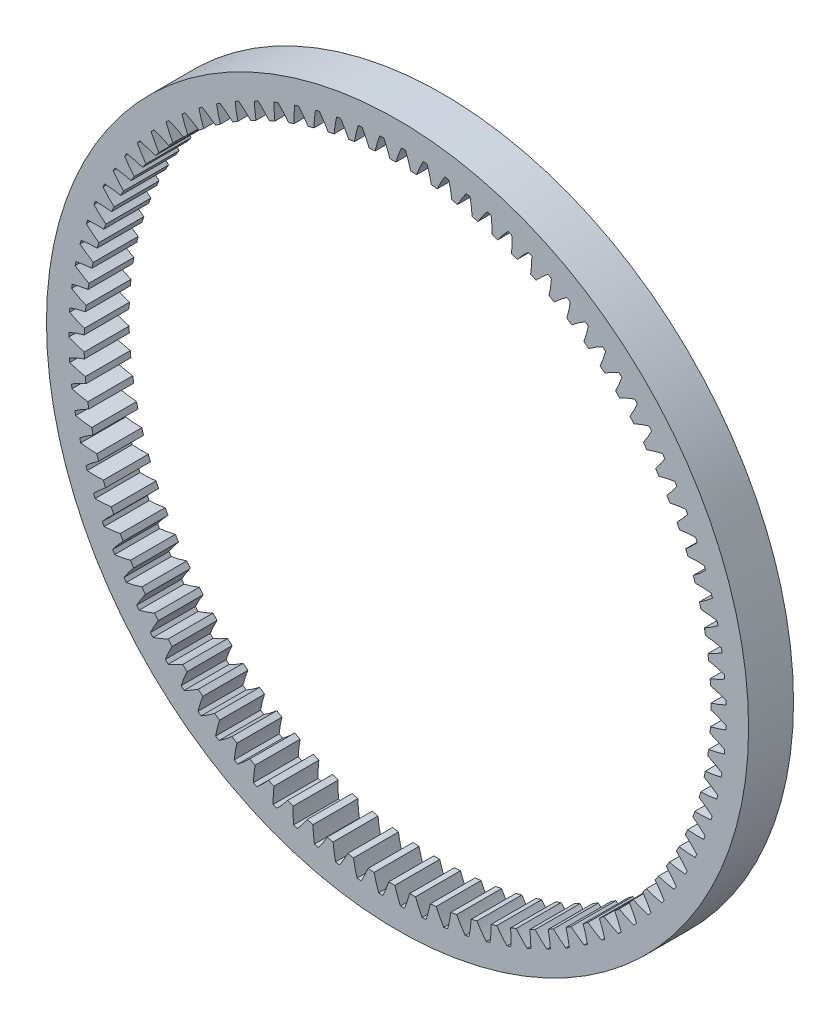
SolidWorks part; units mm, degrees
material "Výchozí"
ref_plane "Rovina XY" through (0, 0, 0) normal (0, 0, 1) x (1, 0, 0)
ref_plane "Rovina XZ" through (0, 0, 0) normal (0, 1, 0) x (1, 0, 0)
ref_plane "Rovina YZ" through (0, 0, 0) normal (1, 0, 0) x (0, 0, -1)
sketch "Skica1" plane through (0, 0, 0) normal (0, 0, 1) x (1, 0, 0)
  line L0 (-7.6722, 0) -> (24.7299, 0) construction
  line L1 (0, 21.5321) -> (0, 42.0656) construction
  line L2 (0, 0) -> (71.2421, 1.0619)
  line L3 (0, 0) -> (71.168, 3.4168)
  line L4 (0, 0) -> (73.0889, 2.2986) construction
  circle A0 centre (0, 0) radius 66.9531
  circle A1 centre (0, 0) radius 69.75
  circle A2 centre (0, 0) radius 71.25 construction
  circle A3 centre (0, 0) radius 73.125
  spline S0 degree 4 poles (66.9531, 0) (66.9836, 0.0005) (67.0692, 0.0035) (67.2309, 0.0154) (67.4941, 0.0435) (67.8284, 0.0923) (68.2589, 0.1701) (68.7635, 0.2807) (69.315, 0.422) (69.911, 0.5969) (70.5019, 0.7901) (71.0872, 0.9999) (71.6668, 1.2248) (72.3632, 1.5146) (73.1926, 1.8887) (74.1482, 2.3598) (75.2219, 2.9406) (76.2936, 3.5715) (77.3431, 4.2379) (78.3713, 4.9379) (79.3771, 5.6679) (80.2395, 6.3331) (80.9633, 6.918) (81.5608, 7.4194) (82.0279, 7.8211) (82.5011, 8.2403) (82.9487, 8.645) (83.4258, 9.0903) (83.8376, 9.481) (84.4371, 10.0683) (84.7907, 10.4245) (85.3537, 11.0015) (85.5975, 11.264) (85.8218, 11.5002) (85.8856, 11.5706) (85.9334, 11.6219) (85.9593, 11.6496) knots 0 0 0 0 0 0.005377 0.015084 0.028532 0.04661 0.064855 0.092111 0.119476 0.146842 0.174209 0.201575 0.228941 0.256307 0.307035 0.361767 0.4165 0.471232 0.525964 0.580697 0.635429 0.690161 0.717528 0.744894 0.77226 0.799626 0.826992 0.854358 0.881725 0.909091 0.954545 0.977273 0.988636 0.994318 1 1 1 1 1 construction
  spline S1 degree 4 poles (66.9531, 0) (66.9836, 0.0005) (67.0692, 0.0035) (67.2309, 0.0154) (67.4941, 0.0435) (67.8284, 0.0923) (68.2589, 0.1701) (68.7635, 0.2807) (69.315, 0.422) (69.911, 0.5969) (70.5019, 0.7901) (71.0872, 0.9999) (71.6668, 1.2248) (72.3632, 1.5146) (73.1926, 1.8887) (74.1482, 2.3598) (75.2219, 2.9406) (76.2936, 3.5715) (77.3431, 4.2379) (78.3713, 4.9379) (79.3771, 5.6679) (80.2395, 6.3331) (80.9633, 6.918) (81.5608, 7.4194) (82.0279, 7.8211) (82.5011, 8.2403) (82.9487, 8.645) (83.4258, 9.0903) (83.8376, 9.481) (84.2235, 9.859) (84.4262, 10.06) (84.5261, 10.1599) knots 0 0 0 0 0 0.005377 0.015084 0.028532 0.04661 0.064855 0.092111 0.119476 0.146842 0.174209 0.201575 0.228941 0.256307 0.307035 0.361767 0.4165 0.471232 0.525964 0.580697 0.635429 0.690161 0.717528 0.744894 0.77226 0.799626 0.826992 0.854358 0.881725 0.909091 0.909091 0.909091 0.909091 0.909091
sketch "Skica2" plane through (0, 0, 0) normal (0, 0, 1) x (1, 0, 0)
  circle A0 centre (0, 0) radius 78.125
  circle A1 centre (0, 0) radius 73.125 construction
  circle A2 centre (0, 0) radius 69.75 construction
  circle A3 centre (0, 0) radius 69.75
  dimension "D1" = 5
extrude "Přidat vysunutím1" add sketch "Skica2" along normal mid plane 10
sketch "Skica3" plane through (0, 0, 5) normal (0, 0, 1) x (1, 0, 0)
  line L0 (0, 0) -> (73.0889, 2.2986) construction
  line L1 (0, 0) -> (73.0889, 2.2986) construction
  circle A0 centre (0, 0) radius 69.75 construction
  circle A1 centre (0, 0) radius 73.125 construction
  arc A2 (69.7478, 0.5512) -> (69.6446, 3.8326) centre (0, 0) ccw
  arc A3 (73.1015, 1.8541) -> (73.0735, 2.7431) centre (0, 0) ccw
  spline S0 degree 4 poles (57.0181, 1999.7686) (60.1184, 35.926) (62.5959, 0.6685) (65.0492, -0.218) (67.4941, 0.0435) (67.8284, 0.0923) (68.2589, 0.1701) (68.7635, 0.2807) (69.315, 0.422) (69.911, 0.5969) (70.5019, 0.7901) (71.0872, 0.9999) (71.6668, 1.2248) (72.3632, 1.5146) (73.1926, 1.8887) (74.1482, 2.3598) (75.2219, 2.9406) (76.2936, 3.5715) (77.3431, 4.2379) (78.3713, 4.9379) (79.3771, 5.6679) (80.2395, 6.3331) (80.9633, 6.918) (81.5608, 7.4194) (82.0279, 7.8211) (82.5011, 8.2403) (82.9487, 8.645) (83.4258, 9.0903) (85.4018, 10.9651) (90.1065, 15.8673) (40.7158, -33.1093) (1497.9964, 1424.7513) knots -0.386327 -0.386327 -0.386327 -0.386327 -0.386327 0.005377 0.015084 0.028532 0.04661 0.064855 0.092111 0.119476 0.146842 0.174209 0.201575 0.228941 0.256307 0.307035 0.361767 0.4165 0.471232 0.525964 0.580697 0.635429 0.690161 0.717528 0.744894 0.77226 0.799626 0.826992 0.854358 0.881725 1.324891 1.324891 1.324891 1.324891 1.324891 only from (66.9531, 0) to (84.5261, 10.1599) construction
  spline S1 degree 4 poles (69.7478, 0.5512) (69.8628, 0.5858) (70.1259, 0.6672) (70.5352, 0.8021) (71.0872, 0.9999) (71.6668, 1.2248) (72.2437, 1.4649) (72.6728, 1.6552) (72.958, 1.7866) (73.1015, 1.8541) knots 0.125702 0.125702 0.125702 0.125702 0.125702 0.146842 0.174209 0.201575 0.228941 0.256307 0.284234 0.284234 0.284234 0.284234 0.284234
  spline S2 degree 4 poles (69.6446, 3.8326) (69.7615, 3.8053) (70.0293, 3.7406) (70.4462, 3.6317) (71.0095, 3.469) (71.6021, 3.281) (72.1929, 3.0776) (72.6332, 2.9146) (72.926, 2.8013) (73.0735, 2.7431) knots 0.125702 0.125702 0.125702 0.125702 0.125702 0.146842 0.174209 0.201575 0.228941 0.256307 0.284234 0.284234 0.284234 0.284234 0.284234
extrude "Odebrat vysunutím2" cut sketch "Skica3" against normal through all
pattern_circular "Kruhové pole1" count 95 over 360 about axis through (0, 0, 5) along (0, 0, -1) of "Odebrat vysunutím2"
equation "\"modul\"= 1.5"
equation "\"počet_zubů\"= 95"
equation "\"úhel_záběru\"= 20"
equation "\"základní kružnice\"= \"modul\" * \"počet_zubů\" * cos ( \"úhel_záběru\" )"
equation "\"roztečná_kružnice\"= \"modul\" * \"počet_zubů\""
equation "\"patni_kruznice\"= \"roztečná_kružnice\" - 2 * \"modul\""
equation "\"hlavova_kruznice\"= \"roztečná_kružnice\" + 2.5 * \"modul\""
equation "\"D1@Skica1\"=\"základní kružnice\""
equation "\"D2@Skica1\"=\"roztečná_kružnice\""
equation "\"D3@Skica1\"=\"patni_kruznice\""
equation "\"D4@Skica1\"=\"hlavova_kruznice\""
equation "\"D5@Skica1\"=180/\"počet_zubů\""
equation "\"D1@Kruhové pole1\"=\"počet_zubů\""
